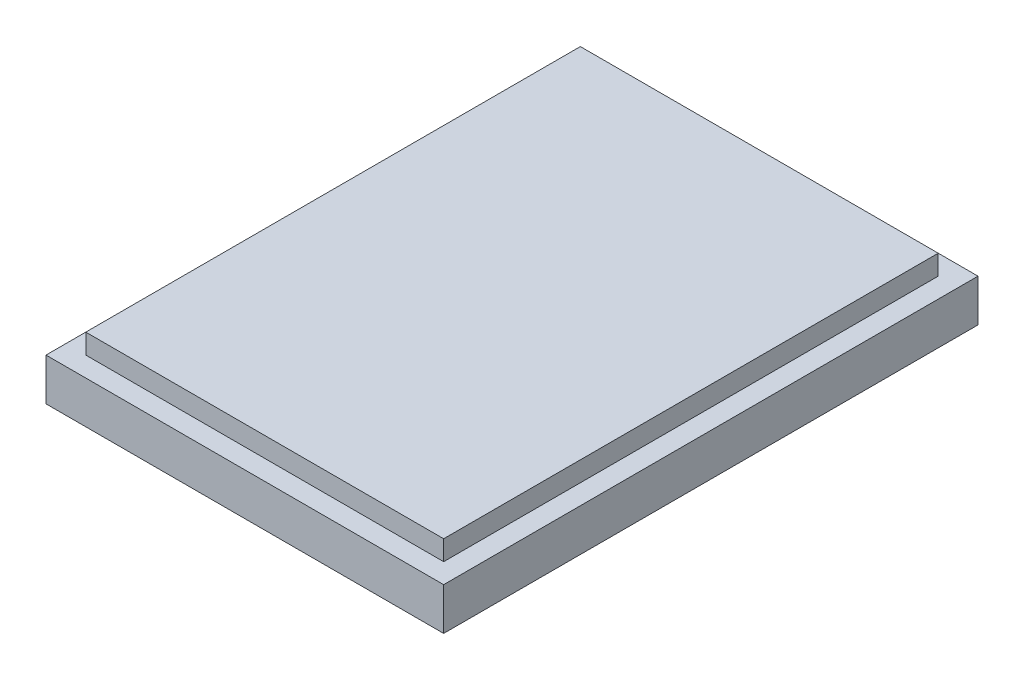
SolidWorks part; units mm, degrees
ref_plane "Front Plane" through (0, 0, 0) normal (0, 0, 1) x (1, 0, 0)
ref_plane "Top Plane" through (0, 0, 0) normal (0, 1, 0) x (1, 0, 0)
ref_plane "Right Plane" through (0, 0, 0) normal (1, 0, 0) x (0, 0, -1)
sketch "Sketch1" plane through (0, 0, 0) normal (0, 1, 0) x (1, 0, 0)
  line L1 (0, 0) -> (50.8, 0)
  line L2 (0, 0) -> (0, 68.2625)
  line L3 (0, 68.2625) -> (50.8, 68.2625)
  line L4 (50.8, 0) -> (50.8, 68.2625)
  dimension "D1" = 68.2625
  dimension "D2" = 50.8
extrude "Boss-Extrude1" add sketch "Sketch1" along normal blind 7.9375
sketch "Sketch2" plane through (0, 7.9375, 0) normal (0, 1, 0) x (1, 0, 0)
  line L0 (0, 0) -> (50.8, 0) construction
  line L1 (50.8, 0) -> (50.8, 68.2625) construction
  line L2 (50.8, 68.2625) -> (0, 68.2625) construction
  line L3 (0, 68.2625) -> (0, 0) construction
  line L4 (0, 0) -> (50.8, 0)
  line L5 (50.8, 0) -> (50.8, 68.2625)
  line L6 (50.8, 68.2625) -> (0, 68.2625)
  line L7 (0, 68.2625) -> (0, 0)
  line L8 (2.54, 65.7225) -> (2.54, 2.54)
  line L9 (2.54, 2.54) -> (48.26, 2.54)
  line L10 (48.26, 2.54) -> (48.26, 65.7225)
  line L11 (48.26, 65.7225) -> (2.54, 65.7225)
  dimension "D1" = 2.54
extrude "Cut-Extrude1" cut sketch "Sketch2" against normal blind 2.54
